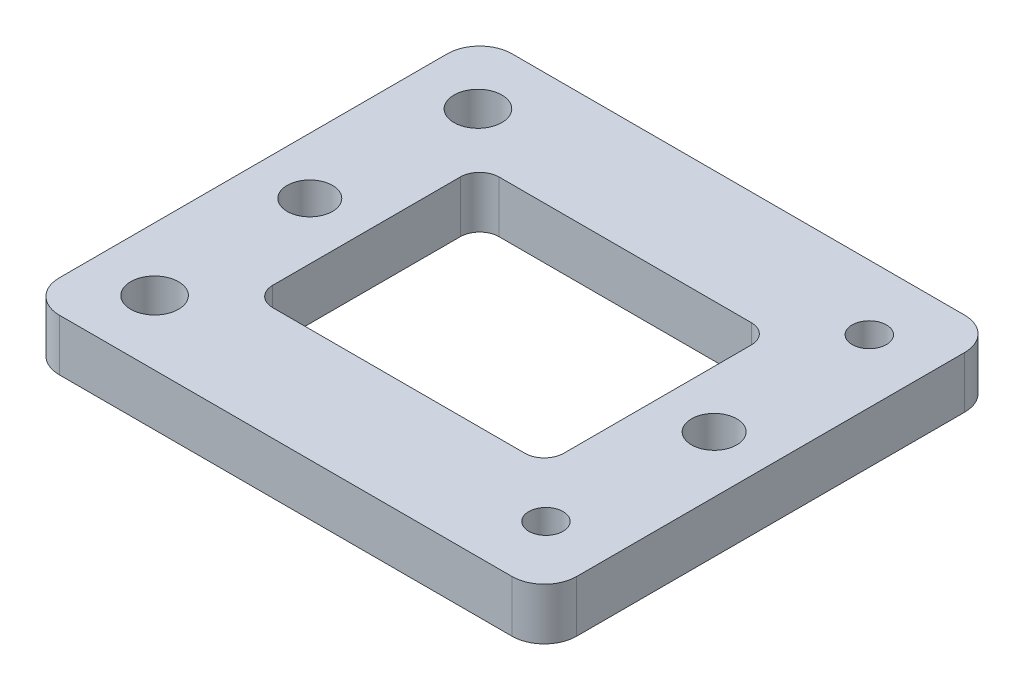
SolidWorks part; units mm, degrees
ref_plane "Alzado" through (0, 0, 0) normal (0, 0, 1) x (1, 0, 0)
ref_plane "Planta" through (0, 0, 0) normal (0, 1, 0) x (1, 0, 0)
ref_plane "Vista lateral" through (0, 0, 0) normal (1, 0, 0) x (0, 0, -1)
sketch "Croquis1" plane through (0, 0, 0) normal (0, 1, 0) x (1, 0, 0)
  line L0 (-35, -35) -> (35, -35)
  line L5 (-19.5, 17.5) -> (19.5, 17.5)
  line L10 (-22.5, 14.5) -> (-22.5, -14.5)
  line L11 (-19.5, -17.5) -> (19.5, -17.5)
  line L12 (22.5, 14.5) -> (22.5, -14.5)
  line L13 (0, 17.5) -> (0, -17.5) construction
  line L14 (-31.2638, 0) -> (-22.5, 0) construction
  line L16 (-40, -30) -> (-40, 30)
  line L17 (-35, 35) -> (35, 35)
  line L18 (40, -30) -> (40, 30)
  line L19 (31.2592, 0) -> (22.5, 0) construction
  line L20 (-30.2641, 24.9974) -> (30.25, 25) construction
  line L21 (-30.2641, 24.9974) -> (-30.2641, -25.0022) construction
  line L22 (30.25, -25) -> (40, -25) construction
  line L23 (0, -17.5) -> (0, -35) construction
  line L24 (0, 17.5) -> (-0.0071, 24.9987) construction
  line L25 (-0.0071, 24.9987) -> (0, 35) construction
  line L26 (-31.2638, 0) -> (-40, 0) construction
  line L27 (31.2592, 0) -> (40, 0) construction
  line L28 (-19.5, 17.5) -> (-30.2641, 17.5) construction
  line L29 (-30.2641, -25.0022) -> (-30.2641, -35) construction
  line L30 (30.25, -25) -> (30.25, -35) construction
  arc A0 (-19.5, -17.5) -> (-22.5, -14.5) centre (-19.5, -14.5) cw
  arc A1 (-19.5, 17.5) -> (-22.5, 14.5) centre (-19.5, 14.5) ccw
  arc A2 (22.5, 14.5) -> (19.5, 17.5) centre (19.5, 14.5) ccw
  arc A3 (19.5, -17.5) -> (22.5, -14.5) centre (19.5, -14.5) ccw
  circle A4 centre (-30.2641, -25.0022) radius 3.7
  circle A5 centre (-30.2641, 24.9974) radius 3.7
  circle A6 centre (-31.2638, 0) radius 3.5
  circle A7 centre (30.25, -25) radius 2.65
  circle A8 centre (30.25, 25) radius 2.65
  circle A9 centre (31.2592, 0) radius 3.5
  arc A10 (-40, 30) -> (-35, 35) centre (-35, 30) cw
  arc A11 (-40, -30) -> (-35, -35) centre (-35, -30) ccw
  arc A12 (40, 30) -> (35, 35) centre (35, 30) ccw
  arc A13 (40, -30) -> (35, -35) centre (35, -30) cw
  arc A14 (-35, -35) -> (-40, -30) centre (-35, -30) cw
  point P0 (0, 0)
  point P47 (0, 0)
  dimension "D3" = 7
  dimension "D4" = 7.4
  dimension "D5" = 5.3
  dimension "D6" = 7
  dimension "D7" = 5
  dimension "D8" = 5
  dimension "D9" = 5
  dimension "D10" = 5
  dimension "D24" = 3
  dimension "D25" = 5.3
  dimension "D26" = 7.4
  dimension "D30" = 10
  dimension "D11" = 45
  dimension "D12" = 35
  dimension "D13" = 49.9997
  dimension "D14" = 10.0013
  dimension "D15" = 17.5
  dimension "D16" = 60.5141
  dimension "D17" = 80
  dimension "D18" = 70
  dimension "D19" = 7.4987
  dimension "D20" = 8.7638
  dimension "D21" = 8.7592
  dimension "D22" = 8.7362
  dimension "D23" = 8.7408
  dimension "D27" = 10.7641
  dimension "D28" = 9.9978
  dimension "D29" = 60.5141
extrude "Saliente-Extruir2" add sketch "Croquis1" along normal blind 8 contours A13 L18 A12 L17 A10 L16 A11 L0 A9 A8 A7 A6 A5 A4 A3 L11 A0 L10 A1 L5 A2 L12
